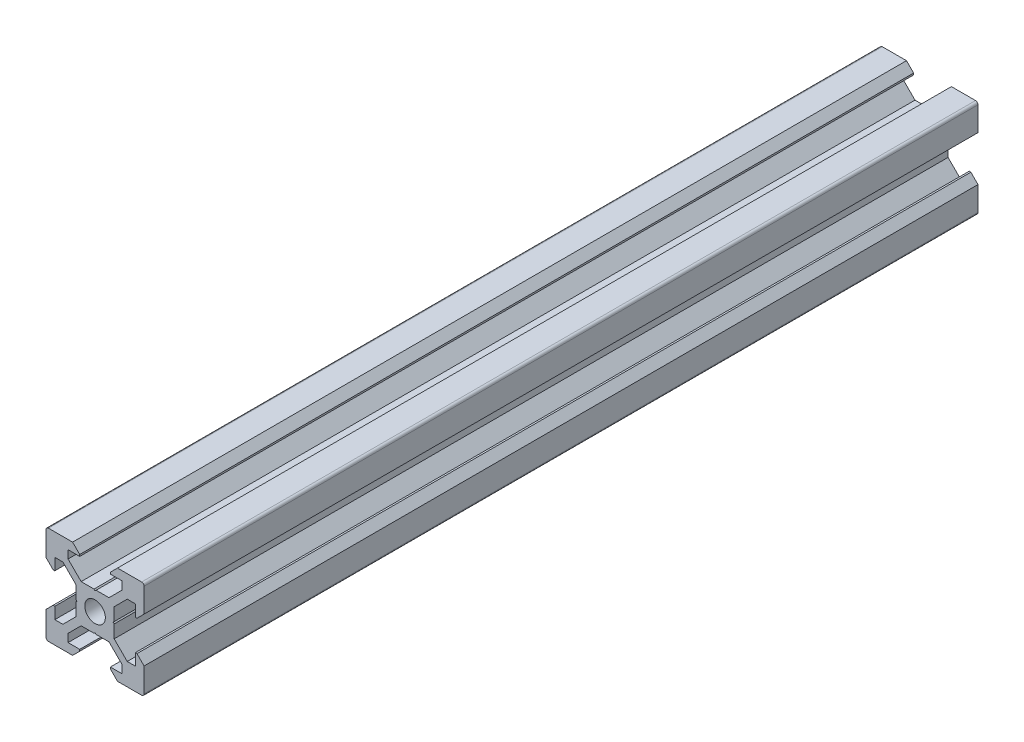
SolidWorks part; units mm, degrees
material "6061-T6 (SS)"
ref_plane "Front Plane" through (0, 0, 0) normal (0, 0, 1) x (1, 0, 0)
ref_plane "Top Plane" through (0, 0, 0) normal (0, 1, 0) x (1, 0, 0)
ref_plane "Right Plane" through (0, 0, 0) normal (1, 0, 0) x (0, 0, -1)
sketch "Sketch1" plane through (0, 0, 0) normal (0, 0, 1) x (1, 0, 0)
  line L1 (9.5, -10) -> (-9.5, -10)
  line L2 (10, -9.5) -> (10, 9.5)
  line L3 (9.5, 10) -> (-9.5, 10)
  line L4 (-10, -9.5) -> (-10, 9.5)
  line L5 (10, -10) -> (-10, 10) construction
  line L6 (10, 10) -> (-10, -10) construction
  circle A0 centre (0, 0) radius 2.1
  arc A1 (-9.5, 10) -> (-10, 9.5) centre (-9.5, 9.5) ccw
  arc A2 (10, 9.5) -> (9.5, 10) centre (9.5, 9.5) ccw
  arc A3 (9.5, -10) -> (10, -9.5) centre (9.5, -9.5) ccw
  arc A4 (-9.5, -10) -> (-10, -9.5) centre (-9.5, -9.5) cw
  point P0 (0, 0)
  line B0 (0, 0) -> (0, 10) construction
  line B1 (0, 3.69) -> (-0.21, 3.9)
  line B2 (-0.21, 3.9) -> (-2.8393, 3.9)
  line B3 (-2.8393, 3.9) -> (-5.5, 6.5607)
  line B4 (-5.5, 6.5607) -> (-5.5, 8.2)
  line B5 (-5.5, 8.2) -> (-3.125, 8.2)
  line B6 (-3.125, 8.2) -> (-3.125, 8.545)
  line B7 (-3.125, 8.545) -> (-4.58, 10)
  line B8 (-4.58, 10) -> (4.58, 10)
  line B9 (0, 0) -> (-5.9132, 5.9132) construction
  line B10 (3.125, 8.545) -> (4.58, 10)
  line B11 (3.125, 8.2) -> (3.125, 8.545)
  line B12 (5.5, 8.2) -> (3.125, 8.2)
  line B13 (5.5, 6.5607) -> (5.5, 8.2)
  line B14 (2.8393, 3.9) -> (5.5, 6.5607)
  line B15 (0.21, 3.9) -> (2.8393, 3.9)
  line B16 (0, 3.69) -> (0.21, 3.9)
  line B17 (0, 0) -> (-10, 0) construction
  line B18 (-3.69, 0) -> (-3.9, -0.21)
  line B19 (-3.9, -0.21) -> (-3.9, -2.8393)
  line B20 (-3.9, -2.8393) -> (-6.5607, -5.5)
  line B21 (-6.5607, -5.5) -> (-8.2, -5.5)
  line B22 (-8.2, -5.5) -> (-8.2, -3.125)
  line B23 (-8.2, -3.125) -> (-8.545, -3.125)
  line B24 (-8.545, -3.125) -> (-10, -4.58)
  line B25 (-10, -4.58) -> (-10, 4.58)
  line B26 (0, 0) -> (-5.9132, -5.9132) construction
  line B27 (-8.545, 3.125) -> (-10, 4.58)
  line B28 (-8.2, 3.125) -> (-8.545, 3.125)
  line B29 (-8.2, 5.5) -> (-8.2, 3.125)
  line B30 (-6.5607, 5.5) -> (-8.2, 5.5)
  line B31 (-3.9, 2.8393) -> (-6.5607, 5.5)
  line B32 (-3.9, 0.21) -> (-3.9, 2.8393)
  line B33 (-3.69, 0) -> (-3.9, 0.21)
  line B34 (0, 0) -> (0, -10) construction
  line B35 (0, -3.69) -> (0.21, -3.9)
  line B36 (0.21, -3.9) -> (2.8393, -3.9)
  line B37 (2.8393, -3.9) -> (5.5, -6.5607)
  line B38 (5.5, -6.5607) -> (5.5, -8.2)
  line B39 (5.5, -8.2) -> (3.125, -8.2)
  line B40 (3.125, -8.2) -> (3.125, -8.545)
  line B41 (3.125, -8.545) -> (4.58, -10)
  line B42 (4.58, -10) -> (-4.58, -10)
  line B43 (0, 0) -> (5.9132, -5.9132) construction
  line B44 (-3.125, -8.545) -> (-4.58, -10)
  line B45 (-3.125, -8.2) -> (-3.125, -8.545)
  line B46 (-5.5, -8.2) -> (-3.125, -8.2)
  line B47 (-5.5, -6.5607) -> (-5.5, -8.2)
  line B48 (-2.8393, -3.9) -> (-5.5, -6.5607)
  line B49 (-0.21, -3.9) -> (-2.8393, -3.9)
  line B50 (0, -3.69) -> (-0.21, -3.9)
  line B51 (0, 0) -> (10, 0) construction
  line B52 (3.69, 0) -> (3.9, 0.21)
  line B53 (3.9, 0.21) -> (3.9, 2.8393)
  line B54 (3.9, 2.8393) -> (6.5607, 5.5)
  line B55 (6.5607, 5.5) -> (8.2, 5.5)
  line B56 (8.2, 5.5) -> (8.2, 3.125)
  line B57 (8.2, 3.125) -> (8.545, 3.125)
  line B58 (8.545, 3.125) -> (10, 4.58)
  line B59 (10, 4.58) -> (10, -4.58)
  line B60 (0, 0) -> (5.9132, 5.9132) construction
  line B61 (8.545, -3.125) -> (10, -4.58)
  line B62 (8.2, -3.125) -> (8.545, -3.125)
  line B63 (8.2, -5.5) -> (8.2, -3.125)
  line B64 (6.5607, -5.5) -> (8.2, -5.5)
  line B65 (3.9, -2.8393) -> (6.5607, -5.5)
  line B66 (3.9, -0.21) -> (3.9, -2.8393)
  line B67 (3.69, 0) -> (3.9, -0.21)
  dimension "D1" = 4.2
  dimension "D3" = 0.5
  dimension "D2" = 20
sketch_block_instance "V Slot 1-4"
sketch_block "V Slot 1" parameters "D1"=10, "D2"=11, "D3"=4.3, "D4"=1.8, "D5"=0.21, "D6"=45, "D7"=9.16, "D8"=1.5, "D9"=6.25
sketch_block_instance "V Slot 1-5"
sketch_block_instance "V Slot 1-6"
sketch_block_instance "V Slot 1-7"
extrude "Boss-Extrude1" add sketch "Sketch1" along normal blind 170 contours B67 B52 B53 B54 B55 B56 B57 B58 L2 A2 L3 B10 B11 B12 B13 B14 B15 B16 B1 B2 B3 B4 B5 B6 B7 A1 L4 B27 B28 B29 B30 B31 B32 B33 B18 B19 B20 B21 B22 B23 B24 A4 L1 B44 B45 B46 B47 B48 B49
